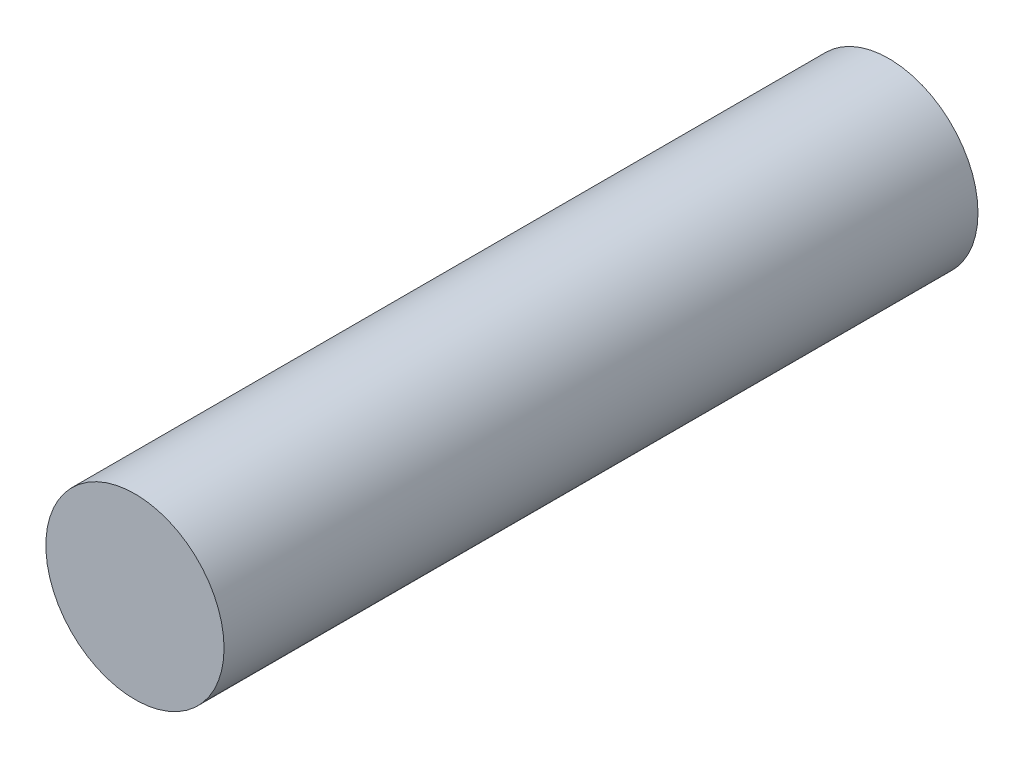
SolidWorks part; units mm, degrees
material "PETG"
ref_plane "Front Plane" through (0, 0, 0) normal (0, 0, 1) x (1, 0, 0)
ref_plane "Top Plane" through (0, 0, 0) normal (0, 1, 0) x (1, 0, 0)
ref_plane "Right Plane" through (0, 0, 0) normal (1, 0, 0) x (0, 0, -1)
sketch "Эскиз1" plane through (0, 0, 0) normal (0, 0, 1) x (1, 0, 0)
  circle A0 centre (0, 0) radius 1.3
  dimension "D1" = 2.6
extrude "Бобышка-Вытянуть1" add sketch "Эскиз1" along normal mid plane 11
